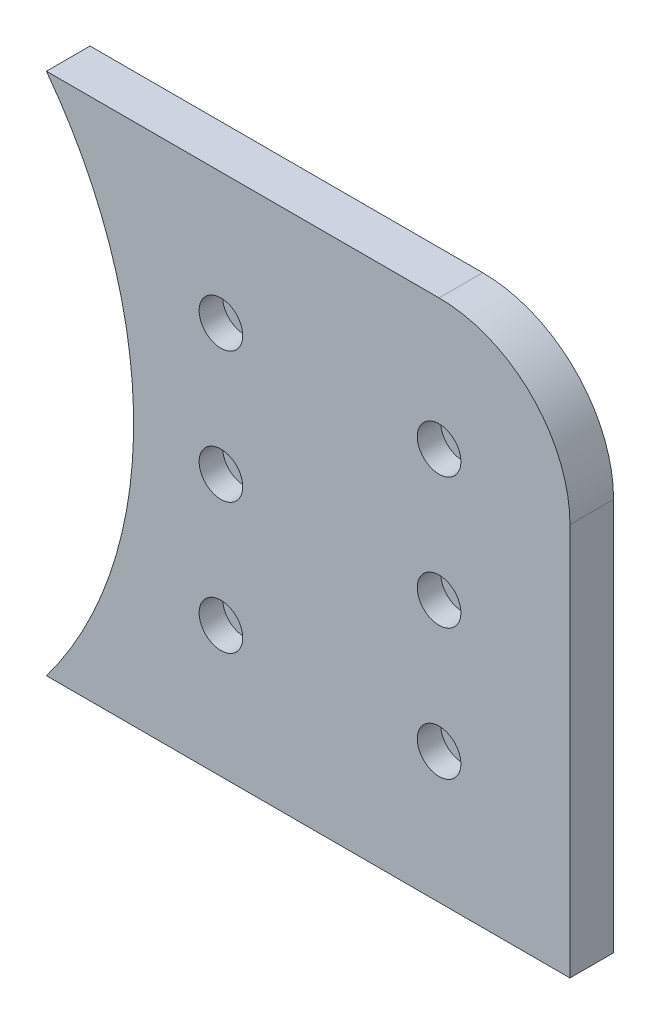
SolidWorks part; units mm, degrees
ref_plane "Vorne" through (0, 0, 0) normal (0, 0, 1) x (1, 0, 0)
ref_plane "Oben" through (0, 0, 0) normal (0, 1, 0) x (1, 0, 0)
ref_plane "Rechts" through (0, 0, 0) normal (1, 0, 0) x (0, 0, -1)
sketch "Skizze1" plane through (0, 0, 0) normal (0, 0, 1) x (1, 0, 0)
  line L1 (-120, 60) -> (0, 60)
  line L3 (-120, -60) -> (0, -60)
  line L4 (0, 60) -> (0, -60)
  arc A0 (-120, 60) -> (-120, -60) centre (-200, 0) cw
  dimension "D1" = 100
  dimension "D2" = 120
extrude "Aufsatz-Linear austragen1" add sketch "Skizze1" along normal mid plane 10
fillet "Verrundung1" radius 30 1 edges at (0, 60, 0)
hole_wizard "Stirnsenkung für M5 Zylinderschraube mit Innensechskant1" positions "Skizze5" profile "Skizze4" counterbore size "M5" standard "ISO" end condition through all
sketch "Skizze5" plane through (0, 0, 5) normal (0, 0, 1) x (1, 0, 0)
  arc A0 (0, 30) -> (-30, 60) centre (-30, 30) ccw construction
  point P0 (-30, 30)
sketch "Skizze4" plane through (-30, 30, 5) normal (1, 0, 0) x (0, -1, 0)
  line L0 (0, 0) -> (0, 10)
  line L1 (0, 10) -> (2.65, 10)
  line L3 (2.65, 10) -> (2.65, 5.4)
  line L4 (2.65, 5.4) -> (5, 5.4)
  line L5 (5, 5.4) -> (5, 0)
  line L7 (5, 0) -> (0, 0)
  line L11 (0, -6.35) -> (0, 107.95) construction
  dimension "Bohrerdurchmesser" = 5.3
  dimension "Bohrungstiefe" = 10
  dimension "Senkdurchmesser2" = 10
  dimension "Senktiefe2" = 5.4
pattern_linear "Lineares Muster1" count 3 spacing 30 along (0, -1, 0) count 2 spacing 50 along (-1, 0, 0) of "Stirnsenkung für M5 Zylinderschraube mit Innensechskant1"
